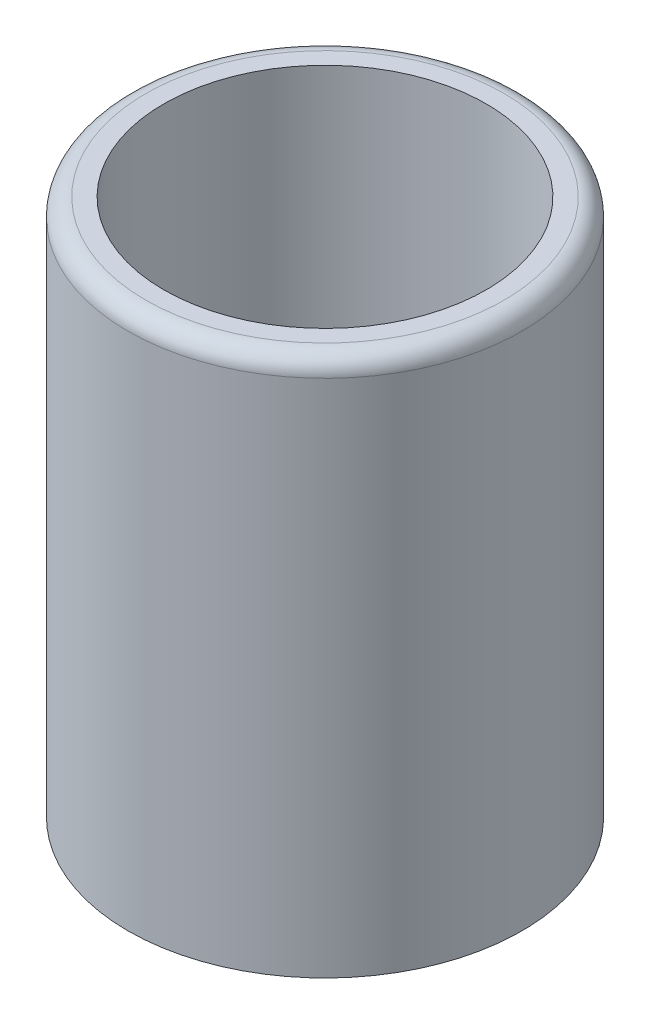
SolidWorks part; units mm, degrees
ref_plane "Plano frontal" through (0, 0, 0) normal (0, 0, 1) x (1, 0, 0)
ref_plane "Plano superior" through (0, 0, 0) normal (0, 1, 0) x (1, 0, 0)
ref_plane "Plano direito" through (0, 0, 0) normal (1, 0, 0) x (0, 0, -1)
sketch "Esboço1" plane through (0, 0, 0) normal (0, 1, 0) x (1, 0, 0)
  circle A0 centre (0, 0) radius 11
  dimension "D1" = 22
extrude "Ressalto-extrusão1" add sketch "Esboço1" along normal blind 30
shell "Casca1" thickness 2
fillet "Filete1" radius 1 1 edges at (0, 30, 11)
